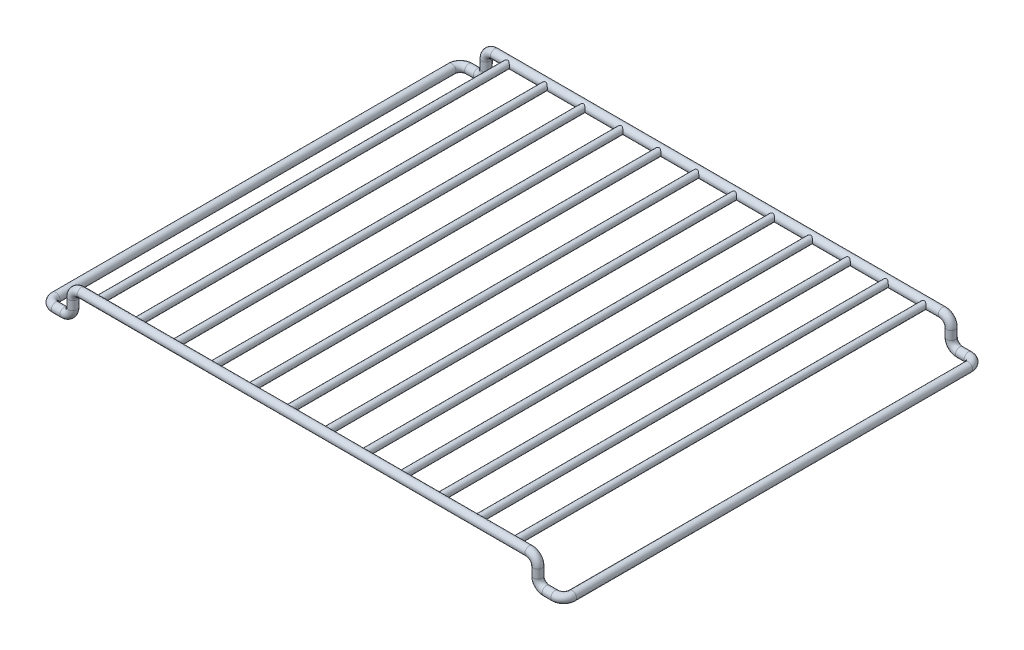
SolidWorks part; units mm, degrees
ref_plane "Front" through (0, 0, 0) normal (0, 0, 1) x (1, 0, 0)
ref_plane "Top" through (0, 0, 0) normal (0, 1, 0) x (1, 0, 0)
ref_plane "Right" through (0, 0, 0) normal (1, 0, 0) x (0, 0, -1)
sketch3d "3DSketch1"
  line L0 (0, 0, 0) -> (130, 0, 0)
  line L1 (135, -5, 0) -> (135, -10, 0)
  line L2 (140, -15, 0) -> (145, -15, 0)
  line L3 (150, -15, -5) -> (150, -15, -235)
  line L4 (145, -15, -240) -> (140, -15, -240)
  line L5 (135, -10, -240) -> (135, -5, -240)
  line L6 (130, 0, -240) -> (0, 0, -240)
  arc A0 (135, -5, -240) -> (130, 0, -240) centre (130, -5, -240) ccw
  arc A1 (135, -10, -240) -> (140, -15, -240) centre (140, -10, -240) ccw
  arc A2 (150, -15, -235) -> (145, -15, -240) centre (145, -15, -235) ccw
  arc A3 (145, -15, 0) -> (150, -15, -5) centre (145, -15, -5) ccw
  arc A4 (140, -15, 0) -> (135, -10, 0) centre (140, -10, 0) ccw
  arc A5 (130, 0, 0) -> (135, -5, 0) centre (130, -5, 0) ccw
  point P9 (65, 0, 0)
  point P10 (135, 0, -240)
  point P11 (130, -5, -235)
  point P14 (135, -15, -240)
  point P16 (140, -10, -235)
  point P20 (150, -15, -240)
  point P21 (145, -10, -235)
  point P24 (150, -15, 0)
  point P25 (145, -10, -5)
  point P28 (135, -15, 0)
  point P29 (140, -10, -5)
  point P32 (135, 0, 0)
  point P33 (130, -5, -5)
  dimension "D5" = 5
  dimension "D1" = 135
  dimension "D2" = 240
  dimension "D3" = 15
  dimension "D4" = 15
sketch "Sketch1" plane through (0, 0, 0) normal (1, 0, 0) x (0, 0, -1)
  circle A0 centre (0, 0) radius 2.5
  dimension "D1" = 5
sweep "Sweep1" add profiles "Sketch1" path "3DSketch1"
sketch "Sketch2" plane through (0, 0, 0) normal (0, 0, 1) x (1, 0, 0)
  line L0 (0, 2.5) -> (0, -2.5) construction
  circle A0 centre (11, 0) radius 2
  dimension "D1" = 4
  dimension "D2" = 11
extrude "Boss-Extrude1" add sketch "Sketch2" against normal up to surface (237.5 mm away) up to face at (0, 0, -237.5)
pattern_linear "LPattern1" count 6 spacing 22 along (1, 0, 0) of "Boss-Extrude1"
mirror "Mirror1" about plane through (0, 0, 0) normal (1, 0, 0) of bodies 103
